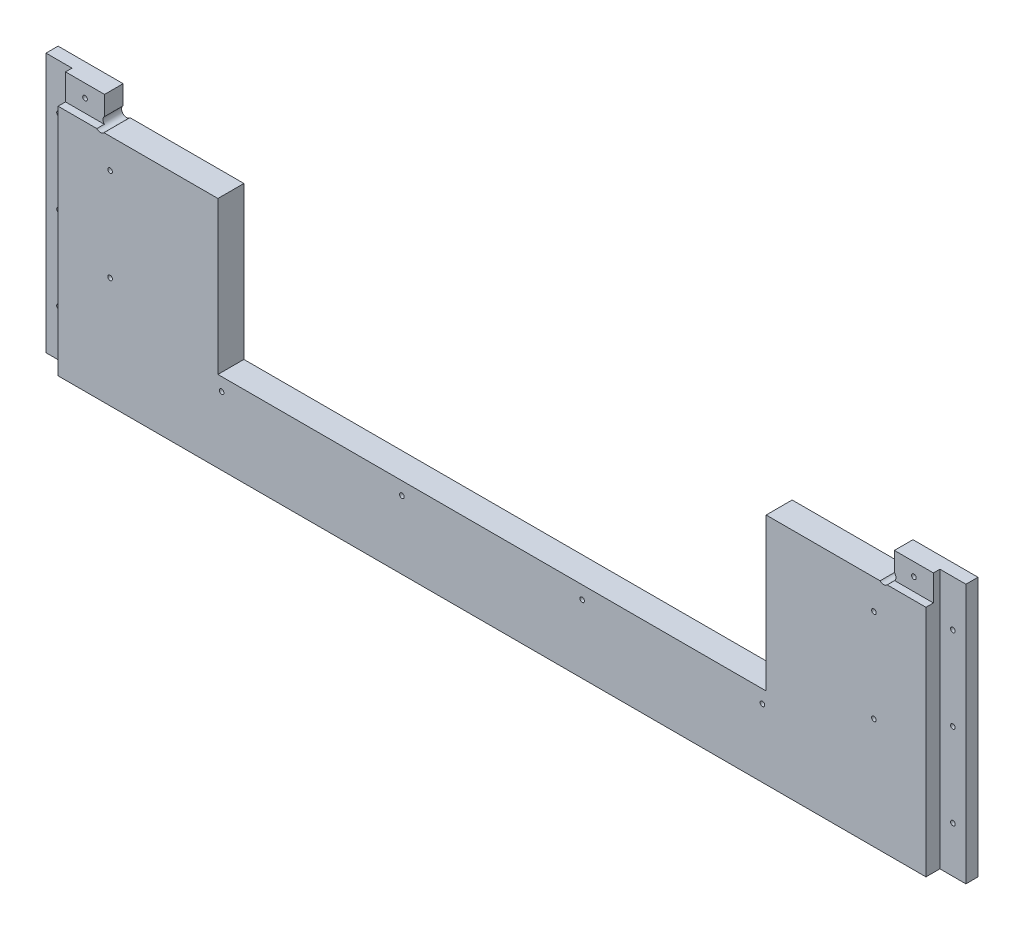
SolidWorks part; units mm, degrees
material "Pine"
ref_plane "Front Plane" through (0, 0, 0) normal (0, 0, 1) x (1, 0, 0)
ref_plane "Top Plane" through (0, 0, 0) normal (0, 1, 0) x (1, 0, 0)
ref_plane "Right Plane" through (0, 0, 0) normal (1, 0, 0) x (0, 0, -1)
sketch "Sketch1" plane through (0, 0, 0) normal (0, 0, 1) x (1, 0, 0)
  line L0 (8932.6508, -5243.5125) -> (10226.1458, -5243.5125)
  line L1 (9086.3208, -4722.0918) -> (10222.9708, -4853.7812)
  line L2 (8914.8708, -6342.0625) -> (10197.5708, -6342.0625)
  line L3 (8914.8708, -5808.6625) -> (10197.5708, -5808.6625)
  line L4 (8919.6333, -5253.0375) -> (10218.2083, -5253.0375)
  line L5 (9134.2633, -4656.1375) -> (9134.2633, -4638.3575)
  line L6 (9091.0833, -4638.3575) -> (9134.2633, -4638.3575)
  line L7 (9091.0833, -4567.2375) -> (9091.0833, -4638.3575)
  line L8 (9134.2633, -4656.1375) -> (9581.3033, -4656.1375)
  line L9 (9091.0833, -4567.2375) -> (9624.4833, -4567.2375)
  line L10 (9581.3033, -4656.1375) -> (9581.3033, -4638.3575)
  line L11 (9581.3033, -4638.3575) -> (9624.4833, -4638.3575)
  line L12 (9624.4833, -4567.2375) -> (9624.4833, -4638.3575)
  line L13 (8932.6508, -5225.7325) -> (9344.9775, -5225.7325)
  line L14 (8932.6508, -5256.2125) -> (8932.6508, -5243.5125)
  line L15 (8911.6958, -5256.2125) -> (8932.6508, -5256.2125)
  line L16 (8914.8708, -4722.0918) -> (9086.3208, -4722.0918)
  line L17 (8911.6958, -4715.5913) -> (8932.6508, -4715.5913)
  line L18 (8914.8708, -6342.0625) -> (8914.8708, -5808.6625)
  line L19 (12082.9917, -4722.0918) -> (10946.3417, -4853.7812)
  line L20 (12236.6617, -5243.5125) -> (10943.1667, -5243.5125)
  line L21 (10951.1042, -5253.0375) -> (12249.6792, -5253.0375)
  line L22 (10838.3917, -5656.2625) -> (11308.2917, -5656.2625)
  line L23 (10838.3917, -5719.7625) -> (11308.2917, -5719.7625)
  line L24 (10838.3917, -5742.5368) -> (11308.2917, -5742.5368)
  line L25 (10806.6417, -6342.0625) -> (11340.0417, -6342.0625)
  line L26 (10803.4667, -6335.7125) -> (11343.2167, -6335.7125)
  line L27 (10803.4667, -6317.9325) -> (11343.2167, -6317.9325)
  line L28 (10943.1667, -5225.7325) -> (11376.4483, -5225.7325)
  line L29 (11506.7292, -4754.5625) -> (10806.6417, -4827.5875)
  line L30 (11506.7292, -4567.2375) -> (11506.7292, -4754.5625)
  line L31 (10806.6417, -4567.2375) -> (10806.6417, -4827.5875)
  line L32 (10806.6417, -4567.2375) -> (11506.7292, -4567.2375)
  line L33 (10235.6708, -6329.3625) -> (10245.1958, -6329.3625)
  line L34 (10245.1958, -6329.3625) -> (10254.7208, -6278.5625)
  line L35 (10302.3458, -6329.3625) -> (10311.8708, -6278.5625)
  line L36 (10302.3458, -6329.3625) -> (10292.8208, -6329.3625)
  line L37 (10245.1958, -5821.3625) -> (10254.7208, -5872.1625)
  line L38 (10235.6708, -5821.3625) -> (10245.1958, -5821.3625)
  line L39 (10292.8208, -5821.3625) -> (10302.3458, -5821.3625)
  line L40 (10302.3458, -5821.3625) -> (10311.8708, -5872.1625)
  line L41 (10235.6708, -5821.3625) -> (10235.6708, -6329.3625)
  line L42 (10254.7208, -5872.1625) -> (10254.7208, -6278.5625)
  line L43 (10311.8708, -5872.1625) -> (10311.8708, -6278.5625)
  line L44 (10292.8208, -5821.3625) -> (10292.8208, -6329.3625)
  line L45 (8932.6508, -5225.7325) -> (8932.6508, -4715.5913)
  line L46 (8911.6958, -4715.5913) -> (8911.6958, -5256.2125)
  line L47 (8914.8708, -5248.275) -> (8914.8708, -4722.0918)
  line L48 (8919.6333, -5253.0375) -> (8914.8708, -5248.275)
  line L49 (8914.8708, -5145.0875) -> (8937.426, -5145.0875)
  line L50 (8914.8708, -5202.2375) -> (8937.426, -5202.2375)
  line L51 (10838.3917, -5656.2625) -> (10838.3917, -5719.7625)
  line L52 (10832.0417, -5736.1868) -> (10856.1717, -5736.1868)
  line L53 (10806.6417, -6342.0625) -> (10806.6417, -5818.7368)
  line L54 (10832.0417, -5649.9125) -> (10856.1717, -5649.9125)
  line L55 (10832.0417, -5726.1125) -> (10856.1717, -5726.1125)
  line L56 (10806.6417, -5818.7368) -> (10833.9015, -5818.7368)
  line L57 (10832.0417, -5806.0442) -> (10851.6815, -5806.0442)
  line L58 (10856.1717, -5801.5541) -> (10856.1717, -5736.1868)
  line L59 (10838.3917, -5814.2467) -> (10838.3917, -5742.5368)
  line L60 (10832.0417, -5806.0442) -> (10832.0417, -5736.1868)
  line L61 (10803.4667, -6317.9325) -> (10803.4667, -6335.7125)
  line L62 (10197.5708, -5808.6625) -> (10197.5708, -6342.0625)
  line L63 (9762.3842, -6348.4125) -> (9762.3842, -5802.3125)
  line L64 (9780.1642, -6348.4125) -> (9762.3842, -6348.4125)
  line L65 (9780.1642, -5802.3125) -> (9780.1642, -6348.4125)
  line L66 (9762.3842, -5802.3125) -> (9780.1642, -5802.3125)
  line L67 (9332.2775, -6348.4125) -> (9332.2775, -5802.3125)
  line L68 (9332.2775, -6348.4125) -> (9350.0575, -6348.4125)
  line L69 (9350.0575, -5802.3125) -> (9350.0575, -6348.4125)
  line L70 (9332.2775, -5802.3125) -> (9350.0575, -5802.3125)
  line L71 (9993.8374, -6061.075) -> (9993.8374, -6045.2418)
  line L72 (9998.5999, -6065.8375) -> (10014.4331, -6065.8375)
  line L73 (9998.5999, -6084.8875) -> (10014.4331, -6084.8875)
  line L74 (9993.8374, -6105.4832) -> (9993.8374, -6089.65)
  line L75 (9974.7874, -6105.4832) -> (9974.7874, -6089.65)
  line L76 (9954.1917, -6084.8875) -> (9970.0249, -6084.8875)
  line L77 (9974.7874, -6061.075) -> (9974.7874, -6045.2418)
  line L78 (9954.1917, -6065.8375) -> (9970.0249, -6065.8375)
  line L79 (10793.9417, -6237.2875) -> (10816.4969, -6237.2875)
  line L80 (10793.9417, -6294.4375) -> (10816.4969, -6294.4375)
  line L81 (10856.1717, -5649.9125) -> (10856.1717, -5726.1125)
  line L82 (10832.0417, -5726.1125) -> (10832.0417, -5649.9125)
  line L83 (10226.1458, -5225.7325) -> (10226.1458, -5243.5125)
  line L84 (10205.1908, -5257.8) -> (10205.1908, -4844.2499)
  line L85 (10230.9083, -4844.2499) -> (10230.9083, -5257.8)
  line L86 (10205.1908, -5257.8) -> (10230.9083, -5257.8)
  line L87 (10205.1908, -4844.2499) -> (10230.9083, -4844.2499)
  line L88 (10946.3417, -5176.8375) -> (10968.8969, -5176.8375)
  line L89 (9349.4676, -5141.9125) -> (9358.2674, -5141.9125)
  line L90 (10946.3417, -5119.6875) -> (10968.8969, -5119.6875)
  line L91 (9929.011, -4660.9635) -> (10066.0807, -4660.9635)
  line L92 (9929.011, -4678.7435) -> (10066.0807, -4678.7435)
  line L93 (10943.1667, -5225.7325) -> (10943.1667, -5243.5125)
  line L94 (10946.3417, -5248.275) -> (10951.1042, -5253.0375)
  line L95 (10946.3417, -5257.8063) -> (10946.3417, -4849.0188)
  line L96 (10964.1217, -5257.8) -> (10964.1217, -4844.2499)
  line L97 (10938.4042, -4844.2499) -> (10938.4042, -5257.8)
  line L98 (10938.4042, -5257.8) -> (10964.1217, -5257.8)
  line L99 (10964.1217, -4844.2499) -> (10938.4042, -4844.2499)
  line L100 (10344.8908, -4560.8875) -> (10369.0208, -4560.8875)
  line L101 (10344.8908, -4560.8875) -> (10369.0208, -4560.8875)
  line L102 (10800.2917, -4560.8875) -> (10824.4217, -4560.8875)
  line L103 (10200.4156, -5119.6875) -> (10222.9708, -5119.6875)
  line L104 (10200.4156, -5176.8375) -> (10222.9708, -5176.8375)
  line L105 (9344.9775, -5146.4026) -> (9344.9775, -5225.7325)
  line L106 (10344.8908, -4560.8875) -> (10344.8908, -4833.9375)
  line L107 (9792.8642, -5225.7325) -> (9792.8642, -5146.4026)
  line L108 (9362.7575, -5225.7325) -> (9775.0842, -5225.7325)
  line L109 (9680.3633, -4761.8396) -> (9680.3633, -4559.9604)
  line L110 (9656.2333, -4559.9604) -> (9680.3633, -4559.9604)
  line L111 (9656.2333, -4761.8396) -> (9680.3633, -4761.8396)
  line L112 (9656.2333, -4761.8396) -> (9656.2333, -4559.9604)
  line L113 (9779.5743, -5141.9125) -> (9788.374, -5141.9125)
  line L114 (10070.5708, -4665.4536) -> (10070.5708, -4674.2534)
  line L115 (9924.5208, -4674.2534) -> (9924.5208, -4665.4536)
  line L116 (12127.4417, -6188.3925) -> (12205.5015, -6188.3925)
  line L117 (12209.9917, -6170.6125) -> (12209.9917, -6183.9024)
  line L118 (9792.8642, -5225.7325) -> (10226.1458, -5225.7325)
  line L119 (9662.5833, -4754.5625) -> (10362.6708, -4827.5875)
  line L120 (9662.5833, -4567.2375) -> (9662.5833, -4754.5625)
  line L121 (10362.6708, -4567.2375) -> (10362.6708, -4827.5875)
  line L122 (9662.5833, -4567.2375) -> (10362.6708, -4567.2375)
  line L123 (10824.4217, -4833.9375) -> (10800.2917, -4833.9375)
  line L124 (10800.2917, -4833.9375) -> (10800.2917, -4560.8875)
  line L125 (10824.4217, -4560.8875) -> (10824.4217, -4833.9375)
  line L126 (10344.8908, -4833.9375) -> (10369.0208, -4833.9375)
  line L127 (10369.0208, -4833.9375) -> (10369.0208, -4560.8875)
  line L128 (10222.9708, -5248.275) -> (10218.2083, -5253.0375)
  line L129 (10222.9708, -5257.8063) -> (10222.9708, -4849.0188)
  line L130 (11734.6544, -5701.375) -> (11739.2301, -5701.375)
  line L131 (9362.7575, -5225.7325) -> (9362.7575, -5146.4026)
  line L132 (9775.0842, -5146.4026) -> (9775.0842, -5225.7325)
  line L133 (11761.3864, -5701.375) -> (11756.8282, -5701.375)
  line L134 (11734.6544, -5693.755) -> (11739.2301, -5693.755)
  line L135 (11761.4039, -5693.755) -> (11756.8282, -5693.755)
  line L136 (11734.6544, -5701.375) -> (11739.2301, -5701.375)
  line L137 (11744.3462, -5721.3024) -> (11744.3462, -5706.4179)
  line L138 (11751.7122, -5721.3024) -> (11751.7122, -5706.4179)
  line L139 (11740.0917, -6170.6125) -> (11740.0917, -6183.9024)
  line L140 (11689.2917, -6188.3925) -> (11822.6417, -6188.3925)
  line L141 (11689.2917, -6348.4093) -> (11689.2917, -6164.2657)
  line L142 (11689.2917, -6164.2657) -> (11746.4417, -6164.2657)
  line L143 (11746.4417, -6164.2657) -> (11746.4417, -6188.3925)
  line L144 (11689.2917, -6164.2657) -> (11746.4417, -6164.2657)
  line L145 (11340.0417, -5818.7368) -> (11340.0417, -6342.0625)
  line L146 (11290.5117, -5726.1125) -> (11314.6417, -5726.1125)
  line L147 (11290.5117, -5649.9125) -> (11290.5117, -5726.1125)
  line L148 (11340.0417, -5818.7368) -> (11312.7818, -5818.7368)
  line L149 (11314.6417, -5806.0442) -> (11295.0018, -5806.0442)
  line L150 (11290.5117, -5801.5541) -> (11290.5117, -5736.1868)
  line L151 (11308.2917, -5814.2467) -> (11308.2917, -5742.5368)
  line L152 (11314.6417, -5806.0442) -> (11314.6417, -5736.1868)
  line L153 (11290.5117, -5736.1868) -> (11314.6417, -5736.1868)
  line L154 (11848.0417, -6267.1325) -> (11962.3417, -6267.1325)
  line L155 (11962.3417, -6267.1325) -> (11962.3417, -6203.6325)
  line L156 (11343.2167, -6317.9325) -> (11343.2167, -6335.7125)
  line L157 (11365.4417, -5656.2625) -> (11365.4417, -5719.7625)
  line L158 (11365.4417, -5656.2625) -> (11479.7417, -5656.2625)
  line L159 (11778.1917, -6071.3937) -> (11802.3217, -6071.3937)
  line L160 (11314.6417, -5726.1125) -> (11314.6417, -5649.9125)
  line L161 (11314.6417, -5649.9125) -> (11290.5117, -5649.9125)
  line L162 (11308.2917, -5719.7625) -> (11308.2917, -5656.2625)
  line L163 (11689.2917, -6348.4093) -> (11713.4217, -6348.4093)
  line L164 (12203.6417, -6164.2657) -> (12260.7917, -6164.2657)
  line L165 (11713.4217, -6348.4093) -> (11713.4217, -6164.2657)
  line L166 (11695.6417, -6342.0625) -> (11695.6417, -6170.6125)
  line L167 (11695.6417, -6048.5337) -> (11699.4517, -6052.3437)
  line L168 (11822.6417, -6292.5325) -> (11822.6417, -6188.3925)
  line L169 (11695.6417, -6342.0625) -> (11695.6417, -6170.6125)
  line L170 (11848.0417, -6203.6325) -> (11962.3417, -6203.6325)
  line L171 (11848.0417, -6203.6325) -> (11848.0417, -6267.1325)
  line L172 (11987.7417, -6267.1325) -> (11987.7417, -6203.6325)
  line L173 (11784.5417, -6077.7437) -> (11784.5417, -6141.2438)
  line L174 (11517.8417, -5656.2625) -> (11632.1417, -5656.2625)
  line L175 (11632.1417, -5656.2625) -> (11632.1417, -5719.7625)
  line L176 (11632.1417, -5719.7625) -> (11517.8417, -5719.7625)
  line L177 (11517.8417, -5719.7625) -> (11517.8417, -5656.2625)
  line L178 (11692.4667, -6028.2137) -> (11692.4667, -6045.9937)
  line L179 (11695.6417, -5979.3188) -> (11718.1969, -5979.3188)
  line L180 (11695.6417, -5922.1687) -> (11718.1969, -5922.1687)
  line L181 (11821.0415, -5722.9375) -> (11821.0415, -5943.6)
  line L182 (11687.7042, -5651.5) -> (11701.9917, -5651.5)
  line L183 (11687.7042, -5651.5) -> (11687.7042, -6055.5251)
  line L184 (11687.7042, -6055.5251) -> (11701.9917, -6055.5251)
  line L185 (11701.9917, -6055.5251) -> (11701.9917, -5651.5)
  line L186 (11695.6417, -6055.2013) -> (11695.6417, -5649.595)
  line L187 (11695.6417, -5656.2625) -> (11695.6417, -6048.5337)
  line L188 (11695.6417, -6170.6125) -> (11740.0917, -6170.6125)
  line L189 (12203.6417, -6164.2657) -> (12203.6417, -6188.3925)
  line L190 (12254.4417, -6342.0625) -> (12254.4417, -6170.6125)
  line L191 (12129.0419, -5943.6) -> (12129.0419, -5722.9375)
  line L192 (12254.4417, -6048.5337) -> (12250.6317, -6052.3437)
  line L193 (12257.6167, -6045.9937) -> (12257.6167, -6028.2137)
  line L194 (12248.0917, -5651.5) -> (12262.3792, -5651.5)
  line L195 (12262.3792, -5651.5) -> (12262.3792, -6055.5251)
  line L196 (12262.3792, -6055.5251) -> (12248.0917, -6055.5251)
  line L197 (12248.0917, -6055.5251) -> (12248.0917, -5651.5)
  line L198 (12254.4417, -6141.2438) -> (12254.4417, -6077.7437)
  line L199 (12236.6617, -6164.2657) -> (12260.7917, -6164.2657)
  line L200 (12102.0417, -6267.1325) -> (11987.7417, -6267.1325)
  line L201 (11330.1865, -6237.2875) -> (11352.7417, -6237.2875)
  line L202 (11330.1865, -6294.4375) -> (11352.7417, -6294.4375)
  line L203 (11474.6617, -5851.8425) -> (11492.4417, -5851.8425)
  line L204 (11474.6617, -5808.6625) -> (11474.6617, -5851.8425)
  line L205 (11403.5417, -5808.6625) -> (11474.6617, -5808.6625)
  line L206 (11492.4417, -5851.8425) -> (11492.4417, -6298.8825)
  line L207 (11403.5417, -6342.0625) -> (11403.5417, -5808.6625)
  line L208 (11474.6617, -6298.8825) -> (11492.4417, -6298.8825)
  line L209 (11474.6617, -6342.0625) -> (11474.6617, -6298.8825)
  line L210 (11403.5417, -6342.0625) -> (11474.6617, -6342.0625)
  line L211 (11619.4417, -5851.8425) -> (11601.6617, -5851.8425)
  line L212 (11601.6617, -5808.6625) -> (11601.6617, -5851.8425)
  line L213 (11530.5417, -5808.6625) -> (11601.6617, -5808.6625)
  line L214 (11619.4417, -5851.8425) -> (11619.4417, -6298.8825)
  line L215 (11530.5417, -6342.0625) -> (11530.5417, -5808.6625)
  line L216 (11619.4417, -6298.8825) -> (11601.6617, -6298.8825)
  line L217 (11601.6617, -6342.0625) -> (11601.6617, -6298.8825)
  line L218 (11530.5417, -6342.0625) -> (11601.6617, -6342.0625)
  line L219 (11479.7417, -5719.7625) -> (11479.7417, -5656.2625)
  line L220 (11365.4417, -5719.7625) -> (11479.7417, -5719.7625)
  line L221 (11778.1917, -6147.5937) -> (11802.3217, -6147.5937)
  line L222 (11802.3217, -6071.3937) -> (11802.3217, -6147.5937)
  line L223 (11778.1917, -6147.5937) -> (11778.1917, -6071.3937)
  line L224 (12254.4417, -5922.1687) -> (12231.8865, -5922.1687)
  line L225 (12254.4417, -5979.3188) -> (12231.8865, -5979.3188)
  line L226 (12254.4417, -6055.2013) -> (12254.4417, -5649.595)
  line L227 (12254.4417, -6048.5337) -> (12254.4417, -5656.2625)
  line L228 (11841.6917, -5702.2873) -> (12108.3917, -5702.2873)
  line L229 (11822.6417, -6292.5325) -> (12127.4417, -6292.5325)
  line L230 (12127.4417, -6292.5325) -> (12127.4417, -6188.3925)
  line L231 (12254.4417, -6170.6125) -> (12209.9917, -6170.6125)
  line L232 (11695.6417, -6342.0625) -> (12254.4417, -6342.0625)
  line L233 (12236.6617, -6348.4093) -> (12260.7917, -6348.4093)
  line L234 (12260.7917, -6348.4093) -> (12260.7917, -6164.2657)
  line L235 (12236.6617, -6348.4093) -> (12236.6617, -6164.2657)
  line L236 (12102.0417, -6203.6325) -> (12102.0417, -6267.1325)
  line L237 (11987.7417, -6203.6325) -> (12102.0417, -6203.6325)
  line L238 (12236.6617, -6147.5937) -> (12236.6617, -6071.3937)
  line L239 (12203.6417, -6188.3925) -> (12260.7917, -6188.3925)
  line L240 (11098.7417, -4665.4536) -> (11098.7417, -4674.2534)
  line L241 (11394.2283, -5146.4026) -> (11394.2283, -5225.7325)
  line L242 (11376.4483, -5225.7325) -> (11376.4483, -5146.4026)
  line L243 (11394.2283, -5225.7325) -> (11806.555, -5225.7325)
  line L244 (11841.6917, -5964.2502) -> (12108.3917, -5964.2502)
  line L245 (12236.6617, -6147.5937) -> (12260.7917, -6147.5937)
  line L246 (12236.6617, -5256.2125) -> (12236.6617, -5243.5125)
  line L247 (12260.7917, -6147.5937) -> (12260.7917, -6071.3937)
  line L248 (12260.7917, -6071.3937) -> (12236.6617, -6071.3937)
  line L249 (12254.4417, -6077.7437) -> (11784.5417, -6077.7437)
  line L250 (11784.5417, -6141.2438) -> (12254.4417, -6141.2438)
  line L252 (12254.4417, -5656.2625) -> (11695.6417, -5656.2625)
  line L253 (11699.4517, -6052.3437) -> (12250.6317, -6052.3437)
  line L254 (11692.4667, -6045.9937) -> (12257.6167, -6045.9937)
  line L255 (11692.4667, -6028.2137) -> (12257.6167, -6028.2137)
  line L256 (11824.335, -5146.4026) -> (11824.335, -5225.7325)
  line L257 (11811.0451, -5141.9125) -> (11819.8449, -5141.9125)
  line L258 (11244.7917, -4674.2534) -> (11244.7917, -4665.4536)
  line L259 (11806.555, -5225.7325) -> (11806.555, -5146.4026)
  line L260 (11488.9492, -4761.8396) -> (11488.9492, -4559.9604)
  line L261 (11488.9492, -4559.9604) -> (11513.0792, -4559.9604)
  line L262 (11488.9492, -4761.8396) -> (11513.0792, -4761.8396)
  line L263 (11513.0792, -4761.8396) -> (11513.0792, -4559.9604)
  line L264 (11240.3015, -4660.9635) -> (11103.2318, -4660.9635)
  line L265 (11103.2318, -4678.7435) -> (11240.3015, -4678.7435)
  line L266 (12236.6617, -5225.7325) -> (12236.6617, -4715.5913)
  line L267 (12257.6167, -4715.5913) -> (12257.6167, -5256.2125)
  line L268 (12254.4417, -5248.275) -> (12254.4417, -4722.0918)
  line L269 (12236.6617, -5225.7325) -> (11824.335, -5225.7325)
  line L270 (12035.0492, -4656.1375) -> (12035.0492, -4638.3575)
  line L271 (12078.2292, -4638.3575) -> (12035.0492, -4638.3575)
  line L272 (12078.2292, -4567.2375) -> (12078.2292, -4638.3575)
  line L273 (12035.0492, -4656.1375) -> (11588.0092, -4656.1375)
  line L274 (11544.8292, -4567.2375) -> (12078.2292, -4567.2375)
  line L275 (11588.0092, -4656.1375) -> (11588.0092, -4638.3575)
  line L276 (11544.8292, -4638.3575) -> (11588.0092, -4638.3575)
  line L277 (11544.8292, -4567.2375) -> (11544.8292, -4638.3575)
  line L278 (12249.6792, -5253.0375) -> (12254.4417, -5248.275)
  line L280 (12257.6167, -5256.2125) -> (12236.6617, -5256.2125)
  line L281 (12231.8865, -5145.0875) -> (12254.4417, -5145.0875)
  line L282 (12231.8865, -5202.2375) -> (12254.4417, -5202.2375)
  line L283 (12236.6617, -4715.5913) -> (12257.6167, -4715.5913)
  line L284 (12082.9917, -4722.0918) -> (12254.4417, -4722.0918)
  line L285 (11380.9385, -5141.9125) -> (11389.7382, -5141.9125)
  circle A0 centre (8923.7608, -4778.9042) radius 1.5875
  circle A1 centre (9062.6598, -4736.3765) radius 2.3685
  circle A2 centre (9051.3958, -6281.7375) radius 22.225
  circle A3 centre (9083.1458, -6249.9875) radius 1.5875
  circle A4 centre (9083.1458, -6313.4875) radius 1.5875
  circle A5 centre (9019.6458, -6249.9875) radius 1.5875
  circle A6 centre (9019.6458, -6313.4875) radius 1.5875
  circle A7 centre (8972.3383, -5202.2375) radius 1.5875
  circle A8 centre (8923.7608, -5015.9708) radius 1.5875
  circle A9 centre (8923.7608, -5134.5042) radius 1.5875
  circle A10 centre (9054.5708, -5234.6225) radius 1.5875
  circle A11 centre (8923.7608, -4897.4375) radius 1.5875
  circle A12 centre (8972.3383, -5087.9375) radius 1.5875
  circle A13 centre (8972.3383, -5145.0875) radius 1.5875
  circle A14 centre (10847.2817, -5668.9625) radius 1.5875
  circle A15 centre (10847.2817, -5707.0625) radius 1.5875
  circle A16 centre (10847.2817, -5755.2368) radius 1.5875
  circle A17 centre (10851.4092, -6237.2875) radius 1.5875
  circle A18 centre (10851.4092, -6294.4375) radius 1.5875
  circle A19 centre (10847.2817, -5793.3442) radius 1.5875
  arc A20 (10833.9015, -5818.7368) -> (10838.3917, -5814.2467) centre (10836.1466, -5816.4918) ccw
  arc A21 (10851.6815, -5806.0442) -> (10856.1717, -5801.5541) centre (10853.9266, -5803.7992) ccw
  circle A22 centre (10882.8417, -6040.4375) radius 1.5875
  circle A23 centre (10882.8417, -6218.2375) radius 1.5875
  circle A24 centre (10882.8417, -5862.6375) radius 1.5875
  circle A25 centre (10908.2417, -6326.8225) radius 1.5875
  circle A26 centre (10908.2417, -6326.8225) radius 1.5875
  circle A27 centre (10851.4092, -6180.1375) radius 1.5875
  circle A28 centre (10815.5317, -4783.4231) radius 1.5875
  circle A29 centre (10815.5317, -4696.9488) radius 1.5875
  circle A30 centre (10815.5317, -4610.4746) radius 1.5875
  circle A31 centre (10979.1323, -4867.0082) radius 2.3685
  circle A32 centre (10190.1802, -4867.0082) radius 2.3685
  circle A33 centre (10955.2317, -4929.9812) radius 1.5875
  circle A34 centre (10955.2317, -5031.5812) radius 1.5875
  circle A35 centre (10214.0808, -4929.9812) radius 1.5875
  circle A36 centre (10214.0808, -5031.5812) radius 1.5875
  circle A37 centre (9341.1675, -6265.8625) radius 1.5875
  circle A38 centre (9771.2742, -5884.8625) radius 1.5875
  circle A39 centre (9771.2742, -6138.8625) radius 1.5875
  circle A40 centre (9771.2742, -6011.8625) radius 1.5875
  arc A41 (10036.2287, -6113.8083) -> (10051.3426, -6111.6033) centre (10042.9639, -6107.0732) ccw
  arc A42 (10051.3426, -6111.6033) -> (10051.3426, -6039.1217) centre (9984.3124, -6075.3625) ccw
  arc A43 (10051.3426, -6039.1217) -> (10036.2287, -6036.9167) centre (10042.9639, -6043.6518) ccw
  arc A44 (10034.5851, -6102.5431) -> (10034.5851, -6048.1819) centre (9984.3124, -6075.3625) ccw
  arc A45 (10034.5851, -6102.5431) -> (10036.2287, -6113.8083) centre (10042.9639, -6107.0732) ccw
  arc A46 (10036.2287, -6036.9167) -> (10034.5851, -6048.1819) centre (10042.9639, -6043.6518) ccw
  arc A47 (9945.8666, -6127.2787) -> (9948.0717, -6142.3927) centre (9952.6018, -6134.0139) ccw
  arc A48 (9948.0717, -6142.3927) -> (10020.5532, -6142.3927) centre (9984.3124, -6075.3625) ccw
  arc A49 (10020.5532, -6142.3927) -> (10022.7583, -6127.2787) centre (10016.0231, -6134.0139) ccw
  arc A50 (9957.1319, -6125.6352) -> (10011.493, -6125.6352) centre (9984.3124, -6075.3625) ccw
  arc A51 (9957.1319, -6125.6352) -> (9945.8666, -6127.2787) centre (9952.6018, -6134.0139) ccw
  arc A52 (10022.7583, -6127.2787) -> (10011.493, -6125.6352) centre (10016.0231, -6134.0139) ccw
  arc A53 (9932.3962, -6036.9167) -> (9917.2822, -6039.1217) centre (9925.661, -6043.6518) ccw
  arc A54 (9917.2822, -6039.1217) -> (9917.2822, -6111.6033) centre (9984.3124, -6075.3625) ccw
  arc A55 (9917.2822, -6111.6033) -> (9932.3962, -6113.8083) centre (9925.661, -6107.0732) ccw
  arc A56 (9934.0398, -6048.1819) -> (9934.0398, -6102.5431) centre (9984.3124, -6075.3625) ccw
  arc A57 (9934.0398, -6048.1819) -> (9932.3962, -6036.9167) centre (9925.661, -6043.6518) ccw
  arc A58 (9932.3962, -6113.8083) -> (9934.0398, -6102.5431) centre (9925.661, -6107.0732) ccw
  arc A59 (9945.8666, -6023.4463) -> (9957.1319, -6025.0898) centre (9952.6018, -6016.7111) ccw
  arc A60 (10011.493, -6025.0898) -> (10022.7583, -6023.4463) centre (10016.0231, -6016.7111) ccw
  arc A61 (10011.493, -6025.0898) -> (9957.1319, -6025.0898) centre (9984.3124, -6075.3625) ccw
  arc A62 (9948.0717, -6008.3323) -> (9945.8666, -6023.4463) centre (9952.6018, -6016.7111) ccw
  arc A63 (10020.5532, -6008.3323) -> (9948.0717, -6008.3323) centre (9984.3124, -6075.3625) ccw
  arc A64 (10022.7583, -6023.4463) -> (10020.5532, -6008.3323) centre (10016.0231, -6016.7111) ccw
  arc A65 (10005.0943, -6187.7574) -> (10096.7073, -6096.1443) centre (9984.3124, -6075.3625) ccw
  arc A66 (9993.8374, -6178.3911) -> (10005.0943, -6187.7574) centre (10003.3624, -6178.3911) ccw
  arc A67 (10001.6306, -6169.0249) -> (10077.9748, -6092.6807) centre (9984.3124, -6075.3625) ccw
  arc A68 (10087.3411, -6084.8875) -> (10077.9748, -6092.6807) centre (10087.3411, -6094.4125) ccw
  arc A69 (10001.6306, -6169.0249) -> (9993.8374, -6178.3911) centre (10003.3624, -6178.3911) ccw
  arc A70 (9963.5306, -6187.7574) -> (9974.7874, -6178.3911) centre (9965.2624, -6178.3911) ccw
  arc A71 (9871.9176, -6096.1443) -> (9963.5306, -6187.7574) centre (9984.3124, -6075.3625) ccw
  arc A72 (9881.2838, -6084.8875) -> (9871.9176, -6096.1443) centre (9881.2838, -6094.4125) ccw
  arc A73 (9890.65, -6092.6807) -> (9966.9943, -6169.0249) centre (9984.3124, -6075.3625) ccw
  arc A74 (9974.7874, -6178.3911) -> (9966.9943, -6169.0249) centre (9965.2624, -6178.3911) ccw
  arc A75 (9890.65, -6092.6807) -> (9881.2838, -6084.8875) centre (9881.2838, -6094.4125) ccw
  arc A76 (9871.9176, -6054.5807) -> (9881.2838, -6065.8375) centre (9881.2838, -6056.3125) ccw
  arc A77 (9963.5306, -5962.9676) -> (9871.9176, -6054.5807) centre (9984.3124, -6075.3625) ccw
  arc A78 (9974.7874, -5972.3339) -> (9963.5306, -5962.9676) centre (9965.2624, -5972.3339) ccw
  arc A79 (9966.9943, -5981.7001) -> (9890.65, -6058.0443) centre (9984.3124, -6075.3625) ccw
  arc A80 (9881.2838, -6065.8375) -> (9890.65, -6058.0443) centre (9881.2838, -6056.3125) ccw
  arc A81 (9966.9943, -5981.7001) -> (9974.7874, -5972.3339) centre (9965.2624, -5972.3339) ccw
  arc A82 (10077.9748, -6058.0443) -> (10087.3411, -6065.8375) centre (10087.3411, -6056.3125) ccw
  arc A83 (9993.8374, -5972.3339) -> (10001.6306, -5981.7001) centre (10003.3624, -5972.3339) ccw
  arc A84 (10077.9748, -6058.0443) -> (10001.6306, -5981.7001) centre (9984.3124, -6075.3625) ccw
  arc A85 (10087.3411, -6065.8375) -> (10096.7073, -6054.5807) centre (10087.3411, -6056.3125) ccw
  arc A86 (10096.7073, -6054.5807) -> (10005.0943, -5962.9676) centre (9984.3124, -6075.3625) ccw
  arc A87 (10005.0943, -5962.9676) -> (9993.8374, -5972.3339) centre (10003.3624, -5972.3339) ccw
  arc A88 (10014.4331, -6065.8375) -> (10018.7361, -6059.0339) centre (10014.4331, -6061.075) ccw
  arc A89 (10018.7361, -6059.0339) -> (10000.641, -6040.9388) centre (9984.3124, -6075.3625) ccw
  arc A90 (10000.641, -6040.9388) -> (9993.8374, -6045.2418) centre (9998.5999, -6045.2418) ccw
  arc A91 (9993.8374, -6061.075) -> (9998.5999, -6065.8375) centre (9998.5999, -6061.075) ccw
  arc A92 (9993.8374, -6105.4832) -> (10000.641, -6109.7862) centre (9998.5999, -6105.4832) ccw
  arc A93 (10000.641, -6109.7862) -> (10018.7361, -6091.6911) centre (9984.3124, -6075.3625) ccw
  arc A94 (10018.7361, -6091.6911) -> (10014.4331, -6084.8875) centre (10014.4331, -6089.65) ccw
  arc A95 (9998.5999, -6084.8875) -> (9993.8374, -6089.65) centre (9998.5999, -6089.65) ccw
  arc A96 (9954.1917, -6084.8875) -> (9949.8888, -6091.6911) centre (9954.1917, -6089.65) ccw
  arc A97 (9949.8888, -6091.6911) -> (9967.9839, -6109.7862) centre (9984.3124, -6075.3625) ccw
  arc A98 (9967.9839, -6109.7862) -> (9974.7874, -6105.4832) centre (9970.0249, -6105.4832) ccw
  arc A99 (9974.7874, -6089.65) -> (9970.0249, -6084.8875) centre (9970.0249, -6089.65) ccw
  arc A100 (9970.0249, -6065.8375) -> (9974.7874, -6061.075) centre (9970.0249, -6061.075) ccw
  arc A101 (9949.8888, -6059.0339) -> (9954.1917, -6065.8375) centre (9954.1917, -6061.075) ccw
  arc A102 (9967.9839, -6040.9388) -> (9949.8888, -6059.0339) centre (9984.3124, -6075.3625) ccw
  arc A103 (9974.7874, -6045.2418) -> (9967.9839, -6040.9388) centre (9970.0249, -6045.2418) ccw
  arc A104 (10096.7073, -6096.1443) -> (10087.3411, -6084.8875) centre (10087.3411, -6094.4125) ccw
  circle A105 centre (9771.2742, -6265.8625) radius 1.5875
  circle A106 centre (9341.1675, -5884.8625) radius 1.5875
  circle A107 centre (9341.1675, -6138.8625) radius 1.5875
  circle A108 centre (9341.1675, -6011.8625) radius 1.5875
  circle A109 centre (11037.2315, -4887.5494) radius 15.0812
  arc A110 (9349.4676, -5141.9125) -> (9344.9775, -5146.4026) centre (9347.2226, -5144.1576) ccw
  arc A111 (9362.7575, -5146.4026) -> (9358.2674, -5141.9125) centre (9360.5124, -5144.1576) ccw
  circle A112 centre (9946.7458, -4669.8535) radius 1.5875
  arc A113 (9924.5208, -4674.2534) -> (9929.011, -4678.7435) centre (9926.7659, -4676.4984) ccw
  circle A114 centre (11003.8092, -5176.8375) radius 1.5875
  circle A115 centre (11003.8092, -5119.6875) radius 1.5875
  circle A116 centre (10353.7808, -4696.9488) radius 1.5875
  circle A117 centre (10353.7808, -4610.4746) radius 1.5875
  circle A118 centre (10353.7808, -4783.4231) radius 1.5875
  circle A119 centre (11003.8092, -5062.5375) radius 1.5875
  circle A120 centre (9353.8675, -5160.9625) radius 1.5875
  circle A121 centre (9638.7708, -5234.6225) radius 1.5875
  circle A122 centre (9671.4733, -4724.1144) radius 1.5875
  circle A123 centre (9671.4733, -4661.3637) radius 1.5875
  circle A124 centre (9671.4733, -4598.6129) radius 1.5875
  arc A125 (9792.8642, -5146.4026) -> (9788.374, -5141.9125) centre (9790.6191, -5144.1576) ccw
  arc A126 (9779.5743, -5141.9125) -> (9775.0842, -5146.4026) centre (9777.3292, -5144.1576) ccw
  circle A127 centre (10048.3458, -4669.8535) radius 1.5875
  arc A128 (10070.5708, -4665.4536) -> (10066.0807, -4660.9635) centre (10068.3258, -4663.2086) ccw
  arc A129 (10066.0807, -4678.7435) -> (10070.5708, -4674.2534) centre (10068.3258, -4676.4984) ccw
  circle A130 centre (9997.5458, -4669.8535) radius 1.5875
  arc A131 (9929.011, -4660.9635) -> (9924.5208, -4665.4536) centre (9926.7659, -4663.2086) ccw
  circle A132 centre (10132.081, -4887.5494) radius 15.0812
  circle A133 centre (10165.5033, -5176.8375) radius 1.5875
  circle A134 centre (10165.5033, -5119.6875) radius 1.5875
  circle A135 centre (9486.3708, -5234.6225) radius 1.5875
  circle A136 centre (10165.5033, -5062.5375) radius 1.5875
  circle A137 centre (9206.9708, -5234.6225) radius 1.5875
  circle A138 centre (10070.5708, -5234.6225) radius 1.5875
  circle A139 centre (9918.1708, -5234.6225) radius 1.5875
  circle A140 centre (9783.9742, -5160.9625) radius 1.5875
  circle A141 centre (9783.9742, -5193.9825) radius 1.5875
  circle A142 centre (9353.8675, -5193.9825) radius 1.5875
  circle A143 centre (11073.3417, -6326.8225) radius 1.5875
  circle A144 centre (11073.3417, -6326.8225) radius 1.5875
  circle A145 centre (11295.2742, -6180.1375) radius 1.5875
  circle A146 centre (11295.2742, -6294.4375) radius 1.5875
  circle A147 centre (11295.2742, -6237.2875) radius 1.5875
  circle A148 centre (11975.0417, -5692.775) radius 3.4925
  circle A149 centre (11263.8417, -5862.6375) radius 1.5875
  arc A150 (11739.2301, -5701.375) -> (11744.3462, -5706.4179) centre (11748.0292, -5697.565) ccw
  arc A151 (11751.7122, -5706.4179) -> (11756.8282, -5701.375) centre (11748.0292, -5697.565) ccw
  arc A152 (11744.3462, -5721.3024) -> (11751.7122, -5721.3024) centre (11748.0292, -5725.505) ccw
  arc A153 (11734.6544, -5693.755) -> (11724.9787, -5697.565) centre (11730.5667, -5697.565) ccw
  arc A154 (11756.8282, -5693.755) -> (11739.2301, -5693.755) centre (11748.0292, -5697.565) ccw
  arc A155 (11724.9787, -5697.565) -> (11734.6544, -5701.375) centre (11730.5667, -5697.565) ccw
  arc A156 (11761.3864, -5701.375) -> (11771.0797, -5697.565) centre (11765.4842, -5697.565) ccw
  arc A157 (11771.0797, -5697.565) -> (11761.4039, -5693.755) centre (11765.4917, -5697.565) ccw
  arc A158 (11740.0917, -6183.9024) -> (11744.5818, -6188.3925) centre (11742.3367, -6186.1474) ccw
  arc A159 (12205.5015, -6188.3925) -> (12209.9917, -6183.9024) centre (12207.7466, -6186.1474) ccw
  circle A160 centre (11299.4017, -5793.3442) radius 1.5875
  arc A161 (11308.2917, -5814.2467) -> (11312.7818, -5818.7368) centre (11310.5367, -5816.4918) ccw
  arc A162 (11290.5117, -5801.5541) -> (11295.0018, -5806.0442) centre (11292.7567, -5803.7992) ccw
  circle A163 centre (11704.5317, -6314.149) radius 1.5875
  circle A164 centre (11748.9817, -6208.7125) radius 1.5875
  circle A165 centre (11263.8417, -6218.2375) radius 1.5875
  circle A166 centre (11263.8417, -6040.4375) radius 1.5875
  circle A167 centre (11238.4417, -6326.8225) radius 1.5875
  circle A168 centre (11238.4417, -6326.8225) radius 1.5875
  circle A169 centre (11299.4017, -5668.9625) radius 1.5875
  circle A170 centre (11299.4017, -5707.0625) radius 1.5875
  circle A171 centre (11726.7567, -6179.5025) radius 1.5875
  circle A172 centre (11704.5317, -6199.3198) radius 1.5875
  circle A173 centre (11748.9817, -6272.2125) radius 1.5875
  circle A174 centre (11704.5317, -6256.7344) radius 1.5875
  circle A175 centre (11299.4017, -5755.2368) radius 1.5875
  circle A176 centre (11913.4467, -6301.4225) radius 1.5875
  circle A177 centre (11790.2567, -6301.4225) radius 1.5875
  circle A178 centre (11793.4317, -6128.5437) radius 1.5875
  circle A179 centre (11753.1092, -5865.0188) radius 1.5875
  circle A180 centre (11809.9417, -6037.1038) radius 1.5875
  circle A181 centre (11809.9417, -6037.1038) radius 1.5875
  circle A182 centre (11753.1092, -5922.1687) radius 1.5875
  circle A183 centre (11975.0417, -5973.7625) radius 3.4925
  circle A184 centre (11975.0417, -6037.1038) radius 1.5875
  circle A185 centre (11753.1092, -5979.3188) radius 1.5875
  circle A186 centre (11975.0417, -6037.1038) radius 1.5875
  arc A187 (11841.6917, -5702.2873) -> (11821.0415, -5722.9375) centre (11841.6917, -5722.9375) ccw
  circle A188 centre (11811.5292, -5833.2687) radius 3.4925
  arc A189 (11821.0415, -5943.6) -> (11841.6917, -5964.2502) centre (11841.6917, -5943.6) ccw
  circle A190 centre (12196.9742, -5865.0188) radius 1.5875
  arc A191 (12129.0419, -5722.9375) -> (12108.3917, -5702.2873) centre (12108.3917, -5722.9375) ccw
  circle A192 centre (12036.6367, -6301.4225) radius 1.5875
  circle A193 centre (12159.8267, -6301.4225) radius 1.5875
  circle A194 centre (12138.5542, -5833.2687) radius 3.4925
  circle A195 centre (12197.2917, -5761.0375) radius 15.0812
  circle A196 centre (11793.4317, -6090.4437) radius 1.5875
  circle A197 centre (12196.9742, -5922.1687) radius 1.5875
  arc A198 (12108.3917, -5964.2502) -> (12129.0419, -5943.6) centre (12108.3917, -5943.6) ccw
  circle A199 centre (12196.9742, -5979.3188) radius 1.5875
  circle A200 centre (12201.1017, -6272.2125) radius 1.5875
  circle A201 centre (12245.5517, -6314.149) radius 1.5875
  circle A202 centre (12245.5517, -6256.7344) radius 1.5875
  circle A203 centre (12201.1017, -6208.7125) radius 1.5875
  circle A204 centre (12223.3267, -6179.5025) radius 1.5875
  circle A205 centre (12245.5517, -6199.3198) radius 1.5875
  circle A206 centre (11171.7667, -4669.8535) radius 1.5875
  circle A207 centre (11222.5667, -4669.8535) radius 1.5875
  arc A208 (11240.3015, -4678.7435) -> (11244.7917, -4674.2534) centre (11242.5466, -4676.4984) ccw
  circle A209 centre (11385.3383, -5193.9825) radius 1.5875
  circle A210 centre (12106.6527, -4736.3765) radius 2.3685
  circle A211 centre (12140.1417, -6037.1038) radius 1.5875
  circle A212 centre (12140.1417, -6037.1038) radius 1.5875
  circle A213 centre (12245.5517, -6090.4437) radius 1.5875
  circle A214 centre (12245.5517, -6128.5437) radius 1.5875
  circle A215 centre (11385.3383, -5160.9625) radius 1.5875
  arc A216 (11824.335, -5146.4026) -> (11819.8449, -5141.9125) centre (11822.0899, -5144.1576) ccw
  arc A217 (11811.0451, -5141.9125) -> (11806.555, -5146.4026) centre (11808.8001, -5144.1576) ccw
  circle A218 centre (11815.445, -5193.9825) radius 1.5875
  circle A219 centre (11815.445, -5160.9625) radius 1.5875
  circle A220 centre (11530.5417, -5234.6225) radius 1.5875
  circle A221 centre (11962.3417, -5234.6225) radius 1.5875
  arc A222 (11244.7917, -4665.4536) -> (11240.3015, -4660.9635) centre (11242.5466, -4663.2086) ccw
  circle A223 centre (11682.9417, -5234.6225) radius 1.5875
  circle A224 centre (11497.8392, -4724.1144) radius 1.5875
  circle A225 centre (11497.8392, -4661.3637) radius 1.5875
  circle A226 centre (11497.8392, -4598.6129) radius 1.5875
  circle A227 centre (11120.9667, -4669.8535) radius 1.5875
  arc A228 (11103.2318, -4660.9635) -> (11098.7417, -4665.4536) centre (11100.9867, -4663.2086) ccw
  arc A229 (11098.7417, -4674.2534) -> (11103.2318, -4678.7435) centre (11100.9867, -4676.4984) ccw
  circle A230 centre (12196.9742, -5202.2375) radius 1.5875
  circle A231 centre (12245.5517, -5015.9708) radius 1.5875
  circle A232 centre (12245.5517, -5134.5042) radius 1.5875
  circle A233 centre (12114.7417, -5234.6225) radius 1.5875
  circle A234 centre (12245.5517, -4897.4375) radius 1.5875
  circle A235 centre (12245.5517, -4778.9042) radius 1.5875
  circle A236 centre (12196.9742, -5087.9375) radius 1.5875
  circle A237 centre (12196.9742, -5145.0875) radius 1.5875
  circle A238 centre (11098.7417, -5234.6225) radius 1.5875
  circle A239 centre (11251.1417, -5234.6225) radius 1.5875
  arc A240 (11380.9385, -5141.9125) -> (11376.4483, -5146.4026) centre (11378.6934, -5144.1576) ccw
  arc A241 (11394.2283, -5146.4026) -> (11389.7382, -5141.9125) centre (11391.9833, -5144.1576) ccw
sketch "Sketch2" plane through (0, 0, 0) normal (0, 0, 1) x (1, 0, 0)
  line L0 (12324.2917, -6347.9762) -> (12324.2917, -6170.6125)
  line L1 (12324.2917, -6170.6125) -> (12279.8417, -6170.6125)
  line L2 (12279.8417, -6170.6125) -> (12279.8417, -6188.3925)
  line L3 (12279.8417, -6188.3925) -> (12197.2917, -6188.3925)
  line L4 (12197.2917, -6188.3925) -> (12197.2917, -6292.5325)
  line L5 (12197.2917, -6292.5325) -> (11822.6417, -6292.5325)
  line L6 (11822.6417, -6292.5325) -> (11822.6417, -6188.3925)
  line L7 (11822.6417, -6188.3925) -> (11740.0917, -6188.3925)
  line L8 (11740.0917, -6188.3925) -> (11740.0917, -6170.6125)
  line L9 (11740.0917, -6170.6125) -> (11695.6417, -6170.6125)
  line L10 (11695.6417, -6170.6125) -> (11695.6417, -6347.9762)
  line L11 (11695.6417, -6347.9762) -> (12324.2917, -6347.9762)
  dimension "D1" = 17.78
  dimension "D2" = 104.14
  dimension "D4" = 628.65
  dimension "D5" = 44.45
  dimension "D6" = 82.55
extrude "Extrude1" add sketch "Sketch2" against normal blind 17.78
sketch "Sketch3" plane through (0, 0, 0) normal (0, 0, 1) x (1, 0, 0)
  line L0 (11740.0917, -6188.3925) -> (11740.0917, -6170.6125)
  line L1 (11740.0917, -6170.6125) -> (11695.6417, -6170.6125)
  line L2 (11695.6417, -6170.6125) -> (11695.6417, -6188.3925)
  line L3 (11695.6417, -6188.3925) -> (11740.0917, -6188.3925)
  line L4 (12279.8417, -6170.6125) -> (12324.2917, -6170.6125)
  line L5 (12324.2917, -6170.6125) -> (12324.2917, -6188.3925)
  line L6 (12324.2917, -6188.3925) -> (12279.8417, -6188.3925)
  line L7 (12279.8417, -6188.3925) -> (12279.8417, -6170.6125)
  line L8 (11695.6417, -6170.6125) -> (11695.6417, -6347.9762) construction
  line L9 (12324.2917, -6347.9762) -> (12324.2917, -6170.6125) construction
  line L10 (12279.8417, -6170.6125) -> (12279.8417, -6188.3925) construction
  line L11 (12279.8417, -6188.3925) -> (12197.2917, -6188.3925) construction
extrude "Cut-Extrude1" cut sketch "Sketch3" against normal blind 5.08
sketch "Sketch4" plane through (0, 0, 0) normal (0, 0, 1) x (1, 0, 0)
  line L0 (11695.6417, -6347.9762) -> (11713.4217, -6347.9762)
  line L1 (11713.4217, -6347.9762) -> (11713.4217, -6170.6125)
  line L2 (11713.4217, -6170.6125) -> (11695.6417, -6170.6125)
  line L3 (11695.6417, -6170.6125) -> (11695.6417, -6347.9762)
  line L4 (12306.5117, -6347.9762) -> (12324.2917, -6347.9762)
  line L5 (12324.2917, -6347.9762) -> (12324.2917, -6170.6125)
  line L6 (12324.2917, -6170.6125) -> (12306.5117, -6170.6125)
  line L7 (12306.5117, -6170.6125) -> (12306.5117, -6347.9762)
  line L8 (11695.6417, -6347.9762) -> (12324.2917, -6347.9762) construction
  line L9 (11695.6417, -6170.6125) -> (11740.0917, -6170.6125) construction
  line L10 (12324.2917, -6170.6125) -> (12279.8417, -6170.6125) construction
  dimension "D1" = 17.78
  dimension "D2" = 17.78
extrude "Cut-Extrude2" cut sketch "Sketch4" against normal blind 9.525
sketch "Sketch5" plane through (0, 0, 0) normal (0, 0, 1) x (1, 0, 0)
  line L0 (11740.0917, -6188.3925) -> (11742.3367, -6186.1474) construction
  line L1 (11822.6417, -6188.3925) -> (11713.4217, -6188.3925) construction
  line L2 (12279.8417, -6188.3925) -> (12277.5966, -6186.1474) construction
  line L3 (12306.5117, -6188.3925) -> (12197.2917, -6188.3925) construction
  line L4 (11948.3717, -6301.4225) -> (12071.5617, -6301.4225) construction
  line L5 (11825.1817, -6301.4225) -> (11948.3717, -6301.4225) construction
  line L6 (12071.5617, -6301.4225) -> (12194.7517, -6301.4225) construction
  line L7 (12009.9667, -6292.5325) -> (12009.9667, -6301.4225) construction
  line L8 (11695.6417, -6259.2944) -> (11713.4217, -6259.2944) construction
  line L9 (12197.2917, -6292.5325) -> (11822.6417, -6292.5325) construction
  line L10 (11748.9817, -6208.7125) -> (11748.9817, -6272.2125) construction
  line L11 (11748.9817, -6240.4625) -> (11822.6417, -6240.4625) construction
  line L12 (11822.6417, -6292.5325) -> (11822.6417, -6188.3925) construction
  line L13 (12270.9517, -6208.7125) -> (12270.9517, -6272.2125) construction
  line L14 (12293.1767, -6188.3925) -> (12293.1767, -6170.6125) construction
  line L15 (12270.9517, -6240.4625) -> (12197.2917, -6240.4625) construction
  line L16 (12197.2917, -6188.3925) -> (12197.2917, -6292.5325) construction
  line L17 (12279.8417, -6188.3925) -> (12306.5117, -6188.3925) construction
  line L18 (12306.5117, -6170.6125) -> (12279.8417, -6170.6125) construction
  line L19 (11726.7567, -6188.3925) -> (11726.7567, -6170.6125) construction
  line L20 (11695.6417, -6170.6125) -> (11695.6417, -6347.9762) construction
  line L21 (11713.4217, -6188.3925) -> (11740.0917, -6188.3925) construction
  line L22 (11740.0917, -6170.6125) -> (11713.4217, -6170.6125) construction
  line L23 (12324.2917, -6259.2944) -> (12306.5117, -6259.2944) construction
  line L24 (12324.2917, -6347.9762) -> (12324.2917, -6170.6125) construction
  line L25 (12306.5117, -6170.6125) -> (12306.5117, -6347.9762) construction
  line L26 (12315.4017, -6316.4444) -> (12315.4017, -6259.2944) construction
  line L27 (12315.4017, -6259.2944) -> (12315.4017, -6202.1444) construction
  line L28 (11713.4217, -6347.9762) -> (11713.4217, -6170.6125) construction
  line L29 (11704.5317, -6316.4444) -> (11704.5317, -6259.2944) construction
  line L30 (11704.5317, -6259.2944) -> (11704.5317, -6202.1444) construction
  circle A0 centre (11704.5317, -6316.4444) radius 1.5875
  circle A1 centre (11704.5317, -6259.2944) radius 1.5875
  circle A2 centre (11704.5317, -6202.1444) radius 1.5875
  circle A3 centre (11726.7567, -6179.5025) radius 1.5875
  circle A4 centre (11748.9817, -6208.7125) radius 1.5875
  circle A5 centre (11748.9817, -6272.2125) radius 1.5875
  circle A6 centre (11825.1817, -6301.4225) radius 1.5875
  circle A7 centre (11948.3717, -6301.4225) radius 1.5875
  circle A8 centre (12071.5617, -6301.4225) radius 1.5875
  circle A9 centre (12194.7517, -6301.4225) radius 1.5875
  circle A10 centre (12315.4017, -6316.4444) radius 1.5875
  circle A11 centre (12315.4017, -6259.2944) radius 1.5875
  circle A12 centre (12270.9517, -6272.2125) radius 1.5875
  circle A13 centre (12270.9517, -6208.7125) radius 1.5875
  circle A14 centre (12315.4017, -6202.1444) radius 1.5875
  circle A15 centre (12293.1767, -6179.5025) radius 1.5875
  circle A16 centre (11742.3367, -6186.1474) radius 3.302
  circle A17 centre (12277.5966, -6186.1474) radius 3.302
  dimension "D1" = 45
  dimension "D5" = 8.89
  dimension "D2" = 3.175
  dimension "D3" = 45
  dimension "D4" = 3.175
  dimension "D6" = 123.19
  dimension "D7" = 63.5
  dimension "D8" = 73.66
  dimension "D9" = 63.5
  dimension "D10" = 73.66
  dimension "D11" = 57.15
  dimension "D12" = 57.15
  dimension "D13" = 57.15
  dimension "D14" = 57.15
extrude "Cut-Extrude3" cut sketch "Sketch5" against normal up to surface (17.78 mm away) up to face at (12009.9667, -6226.4198, -17.78)
